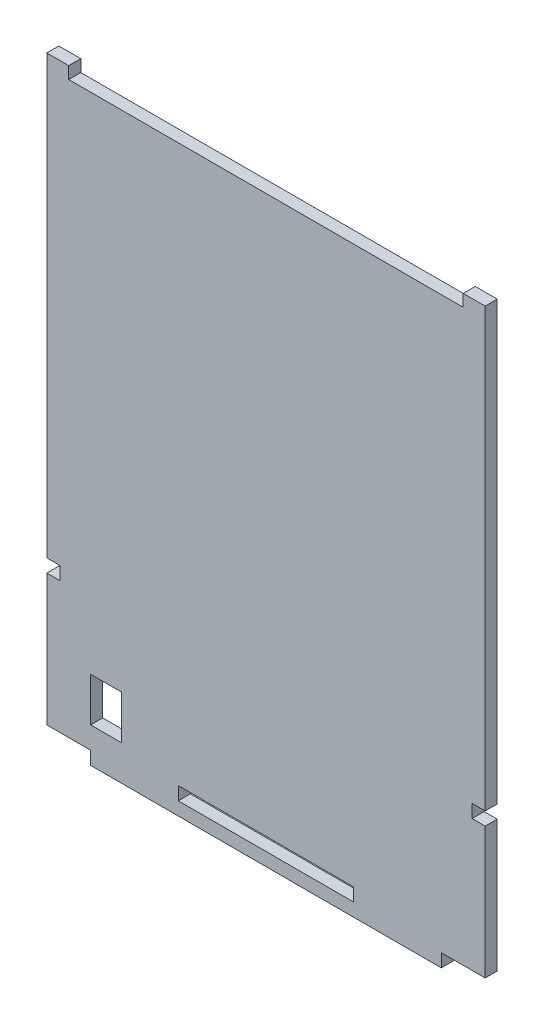
SolidWorks part; units mm, degrees
ref_plane "前视基准面" through (0, 0, 0) normal (0, 0, 1) x (1, 0, 0)
ref_plane "上视基准面" through (0, 0, 0) normal (0, 1, 0) x (1, 0, 0)
ref_plane "右视基准面" through (0, 0, 0) normal (1, 0, 0) x (0, 0, -1)
sketch "草图1" plane through (0, 0, 0) normal (0, 0, 1) x (1, 0, 0)
  line L0 (0, -30) -> (10, -30)
  line L1 (0, 0) -> (100, 0)
  line L2 (0, 3) -> (0, 100)
  line L3 (0, 100) -> (100, 100)
  line L4 (100, 3) -> (100, 100)
  line L5 (0, 0) -> (100, 0)
  line L6 (0, 0) -> (0, -30)
  line L7 (0, -30) -> (100, -30)
  line L8 (100, 0) -> (100, -30)
  line L9 (0, 0) -> (3, 0)
  line L11 (0, 3) -> (3, 3)
  line L12 (3, 0) -> (3, 3)
  line L13 (100, 0) -> (97, 0)
  line L15 (100, 3) -> (97, 3)
  line L16 (97, 0) -> (97, 3)
  line L17 (10, -30) -> (90, -30)
  line L18 (90, -30) -> (100, -30)
  line L19 (50, -30) -> (50, -27)
  line L20 (10, -30) -> (90, -30)
  line L21 (10, -30) -> (10, -33)
  line L22 (10, -33) -> (90, -33)
  line L23 (90, -30) -> (90, -33)
  line L24 (50, -27) -> (70, -27)
  line L25 (70, -27) -> (70, -30)
  line L26 (70, -30) -> (50, -30)
  line L27 (50, -27) -> (30, -27)
  line L28 (30, -27) -> (30, -30)
  line L29 (30, -30) -> (50, -30)
  line L30 (0, 100) -> (0, 102.75)
  line L31 (0, 102.75) -> (5, 102.75)
  line L32 (5, 102.75) -> (5, 100)
  line L33 (100, 100) -> (100, 102.75)
  line L34 (100, 102.75) -> (95, 102.75)
  line L35 (95, 102.4496) -> (95, 100)
  line L36 (95, 102.75) -> (95, 100)
extrude "凸台-拉伸1" add sketch "草图1" along normal blind 2.75 contours L34 L36 L35 L3 L33 | L5 L16 L15 L4 L3 L2 L11 L12 | L32 L31 L30 L3 | L28 L27 L24 L25 L20 L7 L8 L1 L5 L6 L0 | L23 L20 L17 L7 L21 L22
sketch "草图2" plane through (0, 0, 2.75) normal (0, 0, 1) x (1, 0, 0)
  line L0 (10, -30) -> (10, -25)
  line L1 (10, -25) -> (17, -25)
  line L2 (17, -25) -> (17, -15)
  line L3 (17, -15) -> (10, -15)
  line L4 (10, -15) -> (10, -25)
  line L6 (10, -15) -> (17, -15)
  line L7 (10, -15) -> (10, -25)
  line L8 (10, -25) -> (17, -25)
  line L9 (17, -15) -> (17, -25)
extrude "切除-拉伸1" cut sketch "草图2" against normal blind 10 contours L3 L4 L1 L2
